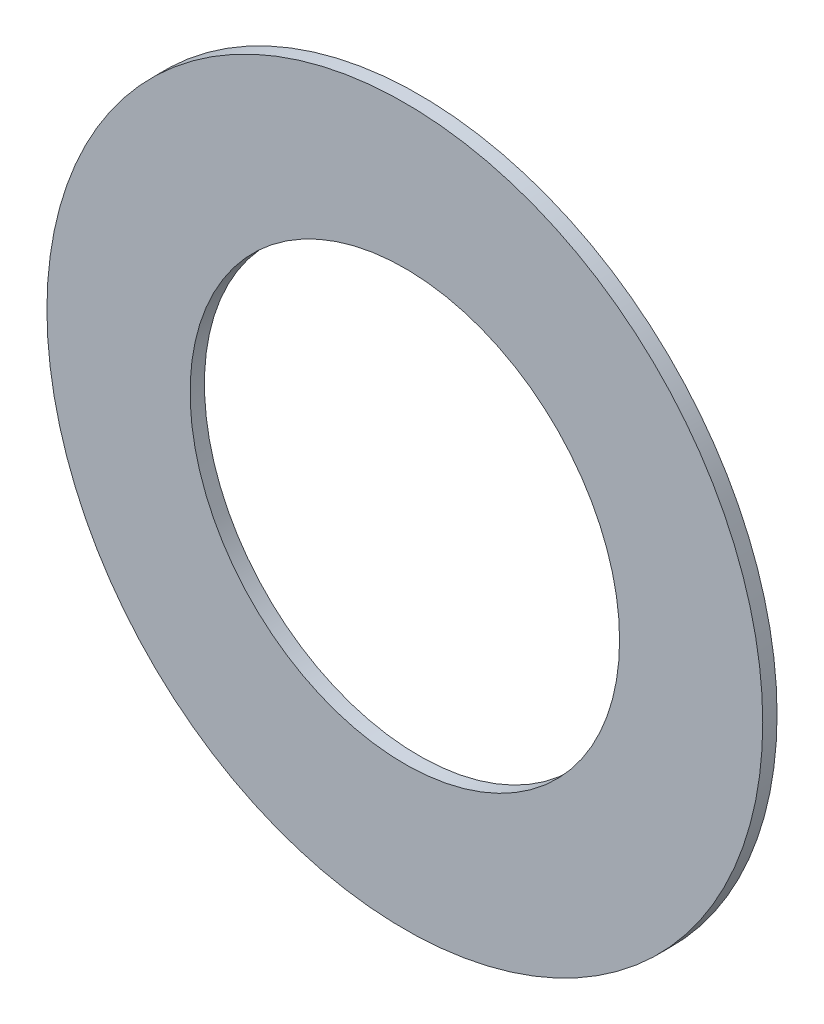
SolidWorks part; units mm, degrees
ref_plane "前视基准面" through (0, 0, 0) normal (0, 0, 1) x (1, 0, 0)
ref_plane "上视基准面" through (0, 0, 0) normal (0, 1, 0) x (1, 0, 0)
ref_plane "右视基准面" through (0, 0, 0) normal (1, 0, 0) x (0, 0, -1)
sketch "草图1" plane through (0, 0, 0) normal (0, 0, 1) x (1, 0, 0)
  circle A0 centre (0, 0) radius 1.5
  circle A1 centre (0, 0) radius 2.5
  dimension "D1" = 3
  dimension "D2" = 5
extrude "凸台-拉伸1" add sketch "草图1" along normal mid plane 0.1
